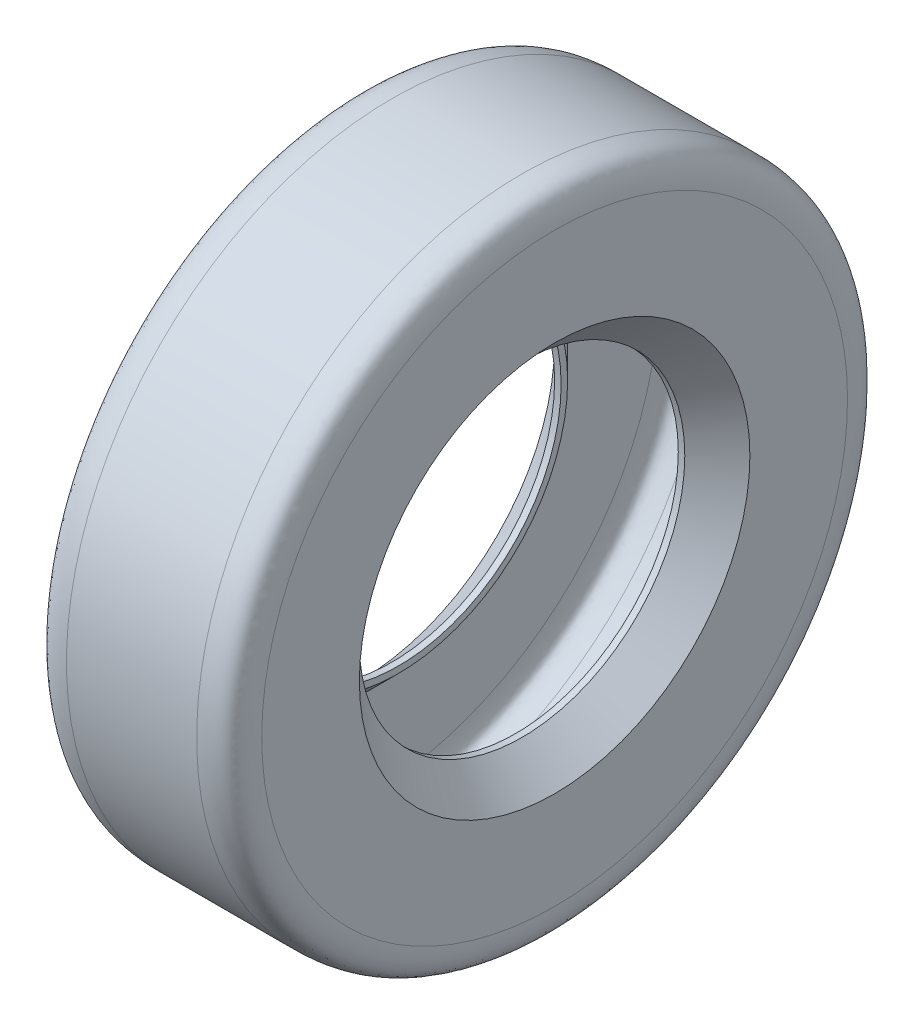
SolidWorks part; units mm, degrees
ref_plane "Front Plane" through (0, 0, 0) normal (0, 0, 1) x (1, 0, 0)
ref_plane "Top Plane" through (0, 0, 0) normal (0, 1, 0) x (1, 0, 0)
ref_plane "Right Plane" through (0, 0, 0) normal (1, 0, 0) x (0, 0, -1)
sketch "Sketch2" plane through (0, 0, 0) normal (0, 0, 1) x (1, 0, 0)
  line L0 (0, 0) -> (0, 63.5) construction
  line L1 (0, 0) -> (0, 63.5) construction
  line L2 (-25.4, 127) -> (25.4, 127)
  line L3 (-22.86, 63.5) -> (-25.4, 63.5) construction
  line L4 (25.4, 124.46) -> (-25.4, 124.46)
  line L5 (-25.4, 63.5) -> (-22.86, 63.5)
  line L7 (0, 0) -> (-33.02, 0) construction
  line L8 (-38.1, 76.2) -> (-25.4, 63.5)
  line L9 (-38.1, 76.2) -> (-38.1, 114.3)
  line L10 (-23.5007, 127) -> (-27.6803, 127) construction
  line L11 (-38.1, 115.2873) -> (-38.1, 111.4202) construction
  line L13 (-22.86, 66.04) -> (-22.86, 63.5)
  line L14 (-22.86, 63.5) -> (-22.86, 78.74) construction
  line L15 (22.86, 63.5) -> (25.4, 63.5) construction
  line L16 (35.56, 78.74) -> (22.86, 66.04)
  line L17 (-35.56, 78.74) -> (-35.56, 114.3)
  line L18 (35.56, 78.74) -> (35.56, 114.3)
  line L19 (22.86, 66.04) -> (22.86, 63.5)
  line L20 (38.1, 76.2) -> (38.1, 114.3)
  line L21 (38.1, 76.2) -> (25.4, 63.5)
  line L22 (25.4, 63.5) -> (22.86, 63.5)
  line L23 (-35.56, 78.74) -> (-22.86, 66.04)
  line L24 (-25.4, 76.2) -> (-38.1, 76.2) construction
  line L25 (-22.86, 78.74) -> (-35.56, 78.74) construction
  line L26 (-25.4, 63.5) -> (-25.4, 76.2) construction
  spline S0 degree 3 poles (-38.1, 114.3) (-38.1, 116.2764) (-38.0644, 127.0224) (-28.6864, 127) (-25.4, 127) knots 0 0 0 0 0.479281 1 1 1 1
  spline S1 degree 1 poles (-35.56, 114.3) (-25.4, 124.46) knots 0 0 1 1 construction
  spline S2 degree 3 poles (-35.56, 114.3) (-35.56, 114.4378) (-35.5598, 114.6992) (-35.5545, 115.3357) (-35.5304, 116.2498) (-35.4485, 117.4909) (-35.2911, 118.7877) (-35.04, 120.0546) (-34.6914, 121.1934) (-34.2493, 122.118) (-33.8076, 122.7058) (-33.234, 123.1866) (-32.2004, 123.7506) (-30.4171, 124.2425) (-28.3012, 124.4237) (-26.6054, 124.4602) (-25.8058, 124.46) (-25.4, 124.46) knots 0 0 0 0 0.03125 0.0625 0.125 0.1875 0.25 0.3125 0.375 0.4375 0.5 0.5625 0.625 0.75 0.875 0.9375 1 1 1 1
  spline S3 degree 3 poles (35.56, 114.3) (35.56, 114.4378) (35.5598, 114.6992) (35.5545, 115.3357) (35.5304, 116.2498) (35.4485, 117.4909) (35.2911, 118.7877) (35.04, 120.0546) (34.6914, 121.1934) (34.2493, 122.118) (33.8076, 122.7058) (33.234, 123.1866) (32.2004, 123.7506) (30.4171, 124.2425) (28.3012, 124.4237) (26.6054, 124.4602) (25.8058, 124.46) (25.4, 124.46) knots 0 0 0 0 0.03125 0.0625 0.125 0.1875 0.25 0.3125 0.375 0.4375 0.5 0.5625 0.625 0.75 0.875 0.9375 1 1 1 1
  spline S4 degree 3 poles (38.1, 114.3) (38.1, 116.2764) (38.0644, 127.0224) (28.6864, 127) (25.4, 127) knots 0 0 0 0 0.479281 1 1 1 1
  dimension "D1" = 25.4
  dimension "D3" = 2.54
  dimension "D5" = 38.1
  dimension "D6" = 2.54
revolve "Revolve4" add sketch "Sketch2" angle 360 about L7
